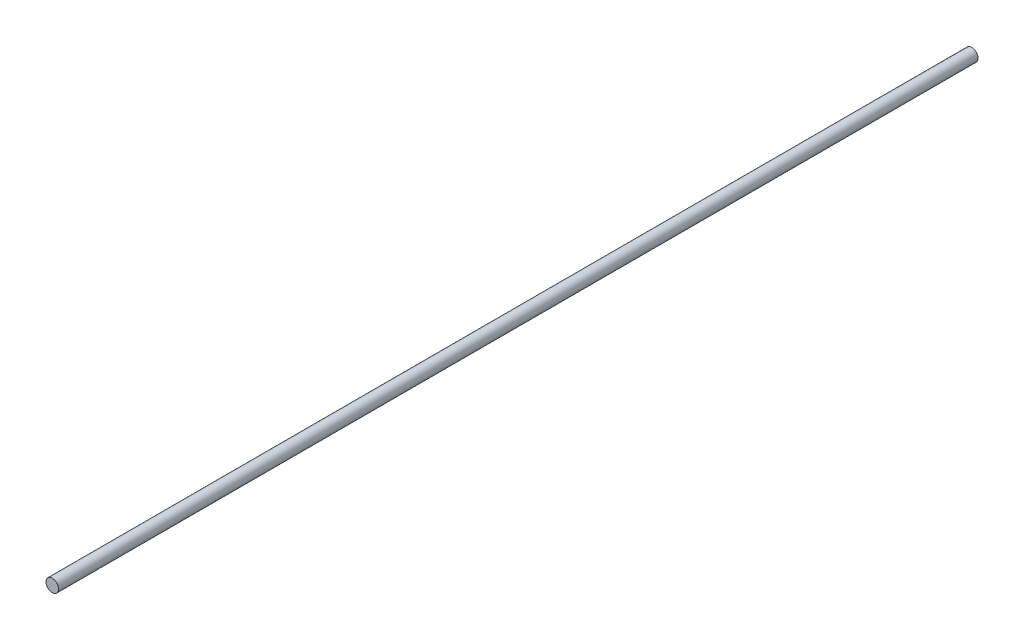
SolidWorks part; units mm, degrees
material "Malleable Cast Iron"
ref_plane "Front Plane" through (0, 0, 0) normal (0, 0, 1) x (1, 0, 0)
ref_plane "Top Plane" through (0, 0, 0) normal (0, 1, 0) x (1, 0, 0)
ref_plane "Right Plane" through (0, 0, 0) normal (1, 0, 0) x (0, 0, -1)
sketch "Sketch1" plane through (0, 0, 0) normal (0, 0, 1) x (1, 0, 0)
  circle A0 centre (0, 0) radius 5
  dimension "D1" = 10
extrude "Boss-Extrude1" add sketch "Sketch1" along normal blind 733 contours A0
